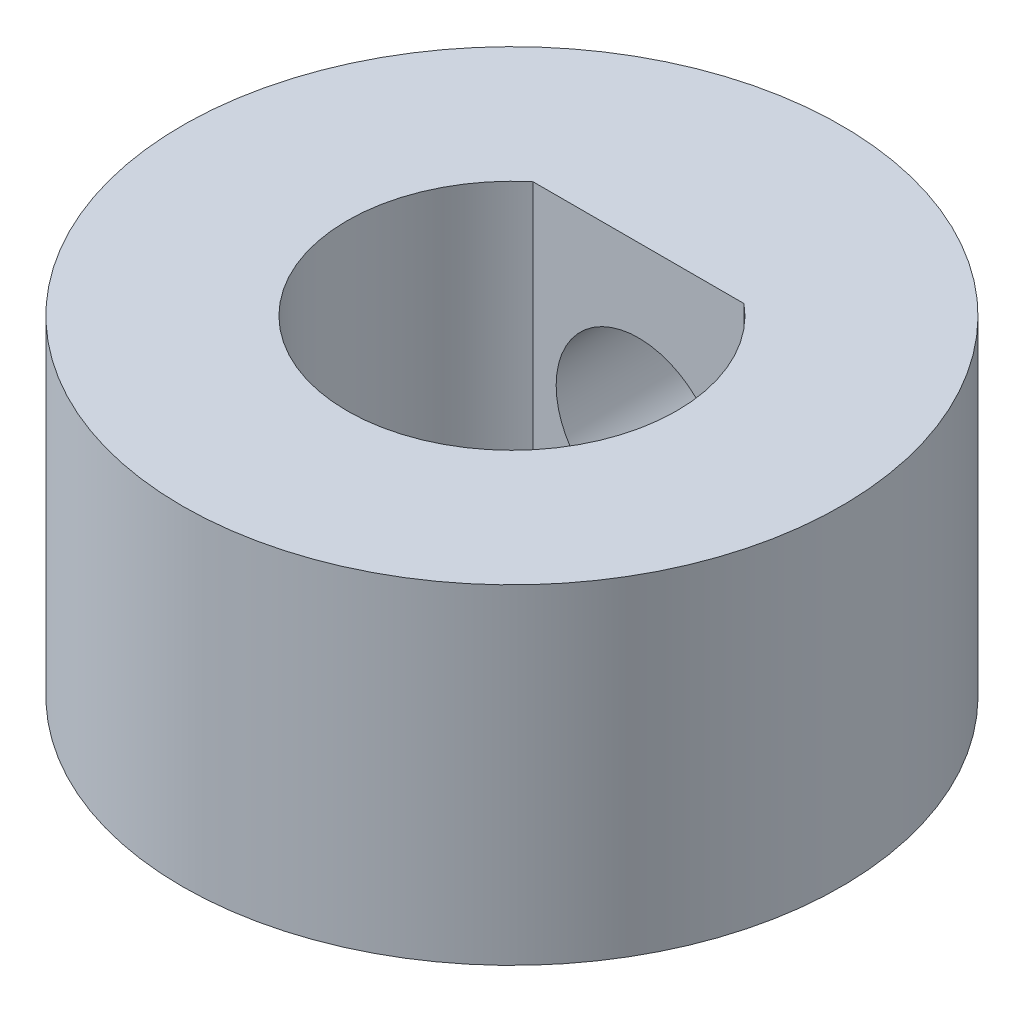
SolidWorks part; units mm, degrees
ref_plane "Front Plane" through (0, 0, 0) normal (0, 0, 1) x (1, 0, 0)
ref_plane "Top Plane" through (0, 0, 0) normal (0, 1, 0) x (1, 0, 0)
ref_plane "Right Plane" through (0, 0, 0) normal (1, 0, 0) x (0, 0, -1)
sketch "Sketch1" plane through (0, 0, 0) normal (0, 1, 0) x (1, 0, 0)
  line L0 (-2.032, 2.4396) -> (2.032, 2.4396)
  circle A0 centre (0, 0) radius 6.35
  circle A1 centre (0, 0) radius 3.175
  dimension "D1" = 6.35
  dimension "D2" = 12.7
  dimension "D3" = 4.064
extrude "Boss-Extrude1" add sketch "Sketch1" along normal blind 6.35 contours L0 A1 | A0 A1
ref_plane "Plane1" through (0, 0, -6.35) normal (0, 0, -1) x (-1, 0, 0)
sketch "Sketch3" plane through (0, 0, -6.35) normal (0, 0, -1) x (-1, 0, 0)
  line L0 (-6.35, 0) -> (6.35, 0) construction
  circle A0 centre (0, 3.175) radius 1.5875
  dimension "D1" = 3.175
  dimension "D2" = 3.175
extrude "Cut-Extrude1" cut sketch "Sketch3" against normal up to next
